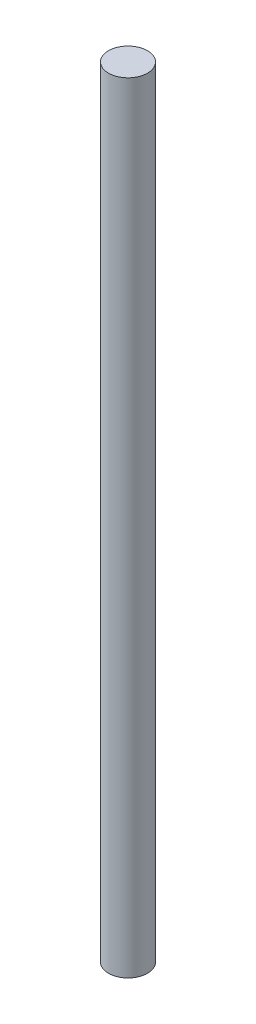
SolidWorks part; units mm, degrees
ref_plane "Front Plane" through (0, 0, 0) normal (0, 0, 1) x (1, 0, 0)
ref_plane "Top Plane" through (0, 0, 0) normal (0, 1, 0) x (1, 0, 0)
ref_plane "Right Plane" through (0, 0, 0) normal (1, 0, 0) x (0, 0, -1)
sketch "草图1" plane through (0, 0, 0) normal (0, 1, 0) x (1, 0, 0)
  circle A0 centre (0, 0) radius 1
extrude "凸台-拉伸2" add sketch "草图1" along normal blind 40
sketch "草图2" plane through (0, 40, 0) normal (0, 1, 0) x (1, 0, 0)
  point P0 (0, 0)
  point P1 (0, 0)
sketch "草图3" plane through (0, 0, 0) normal (0, -1, 0) x (1, 0, 0)
  point P0 (0, 0)
